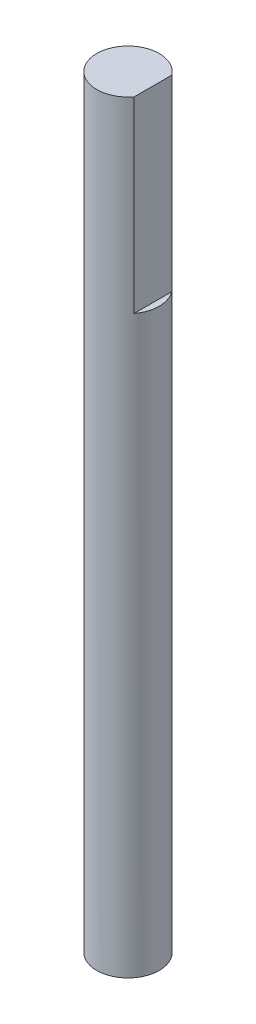
SolidWorks part; units mm, degrees
ref_plane "Front Plane" through (0, 0, 0) normal (0, 0, 1) x (1, 0, 0)
ref_plane "Top Plane" through (0, 0, 0) normal (0, 1, 0) x (1, 0, 0)
ref_plane "Right Plane" through (0, 0, 0) normal (1, 0, 0) x (0, 0, -1)
sketch "Croquis1" plane through (0, 0, 0) normal (0, 1, 0) x (1, 0, 0)
  line L1 (2, 1.5) -> (2, -1.5)
  arc A0 (2, 1.5) -> (2, -1.5) centre (0, 0) ccw
  point P7 (2, 0)
  dimension "D1" = 5
  dimension "D2" = 2
extrude "Saliente-Extruir1" add sketch "Croquis1" along normal blind 15
sketch "Croquis2" plane through (0, 0, 0) normal (0, 1, 0) x (1, 0, 0)
  circle A0 centre (0, 0) radius 2.5
extrude "Saliente-Extruir2" add sketch "Croquis2" against normal blind 46
